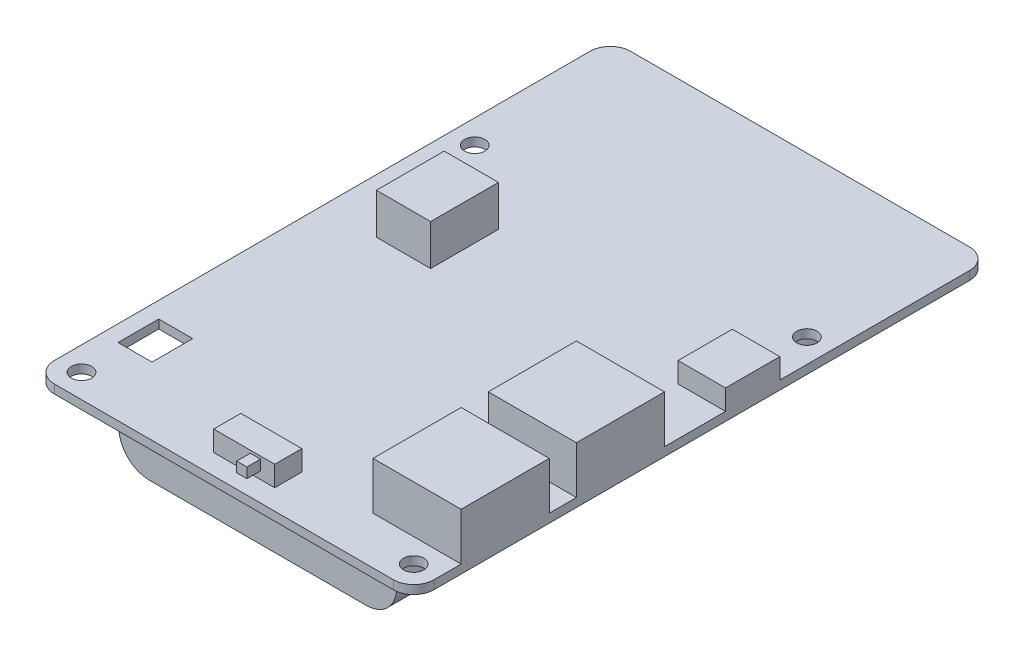
SolidWorks part; units mm, degrees
ref_plane "前基準面" through (0, 0, 0) normal (0, 0, 1) x (1, 0, 0)
ref_plane "上基準面" through (0, 0, 0) normal (0, 1, 0) x (1, 0, 0)
ref_plane "右基準面" through (0, 0, 0) normal (1, 0, 0) x (0, 0, -1)
sketch "草圖1" plane through (0, 0, 0) normal (0, 1, 0) x (1, 0, 0)
  line L1 (-28, -42.5) -> (28, -42.5)
  line L2 (-28, -42.5) -> (-28, 42.5)
  line L3 (-28, 42.5) -> (28, 42.5)
  line L4 (28, -42.5) -> (28, 42.5)
  line L5 (0, 42.5) -> (0, -42.5) construction
  line L6 (-28, 0) -> (28, 0) construction
  circle A0 centre (-24.5, 19) radius 1.5
  circle A1 centre (-24.5, -39) radius 1.5
  circle A2 centre (24.5, -39) radius 1.5
  circle A3 centre (24.5, 19) radius 1.5
  point P0 (0, 0)
  point P8 (0, 0)
  dimension "D3" = 3
  dimension "D1" = 56
  dimension "D2" = 85
  dimension "D4" = 58
  dimension "D5" = 49
  dimension "D6" = 3.5
extrude "填料-伸長1" add sketch "草圖1" along normal blind 1.28
fillet "圓角1" radius 3 4 edges at (-28, 0.64, -42.5) (28, 0.64, -42.5) (28, 0.64, 42.5) (-28, 0.64, 42.5)
sketch "草圖2" plane through (0, 1.28, 0) normal (0, 1, 0) x (1, 0, 0)
  line L0 (28, -39.5) -> (28, 39.5) construction
  line L7 (-25, -42.5) -> (25, -42.5) construction
  line L8 (15, -5.5) -> (28, -5.5)
  line L9 (15, -5.5) -> (15, -18.5)
  line L10 (15, -18.5) -> (28, -18.5)
  line L11 (28, -5.5) -> (28, -18.5)
  line L12 (21.5, -18.5) -> (21.5, -5.5) construction
  line L13 (15, -12) -> (28, -12) construction
  line L14 (15, -22.5) -> (28, -22.5)
  line L15 (15, -22.5) -> (15, -35.5)
  line L16 (15, -35.5) -> (28, -35.5)
  line L17 (28, -22.5) -> (28, -35.5)
  line L18 (21.5, -35.5) -> (21.5, -22.5) construction
  line L19 (15, -29) -> (28, -29) construction
  point P6 (21.5, -12)
  point P10 (21.5, -29)
  dimension "D1" = 13
  dimension "D2" = 13
  dimension "D3" = 13
  dimension "D4" = 13
  dimension "D5" = 30
  dimension "D6" = 7
sketch "草圖3" plane through (0, 1.28, 0) normal (0, 1, 0) x (1, 0, 0)
  line L0 (28, -39.5) -> (28, 39.5) construction
  line L1 (21, 11.5) -> (28, 11.5)
  line L2 (21, 11.5) -> (21, 3.5)
  line L3 (21, 3.5) -> (28, 3.5)
  line L4 (28, 11.5) -> (28, 3.5)
  line L5 (24.5, 3.5) -> (24.5, 11.5) construction
  line L6 (21, 7.5) -> (28, 7.5) construction
  line L7 (15, -5.5) -> (28, -5.5) construction
  point P0 (24.5, 7.5)
  dimension "D1" = 8
  dimension "D2" = 7
  dimension "D3" = 9
sketch "草圖4" plane through (0, 1.28, 0) normal (0, 1, 0) x (1, 0, 0)
  line L0 (-28, 39.5) -> (-28, -39.5) construction
  line L1 (-20, 10) -> (-12, 10)
  line L2 (-20, 10) -> (-20, 0)
  line L3 (-20, 0) -> (-12, 0)
  line L4 (-12, 10) -> (-12, 0)
  line L5 (-16, 0) -> (-16, 10) construction
  line L6 (-20, 5) -> (-12, 5) construction
  line L7 (25, 42.5) -> (-25, 42.5) construction
  point P0 (-16, 5)
  dimension "D1" = 8
  dimension "D2" = 10
  dimension "D3" = 8
  dimension "D4" = 32.5
sketch "草圖5" plane through (0, 1.28, 0) normal (0, 1, 0) x (1, 0, 0)
  line L0 (-25, -42.5) -> (25, -42.5) construction
  line L1 (-4.5, -35.5) -> (4.5, -35.5)
  line L2 (-4.5, -35.5) -> (-4.5, -39.5)
  line L3 (-4.5, -39.5) -> (4.5, -39.5)
  line L4 (4.5, -35.5) -> (4.5, -39.5)
  line L5 (0, -39.5) -> (0, -35.5) construction
  line L6 (-4.5, -37.5) -> (4.5, -37.5) construction
  point P0 (0, -37.5)
  dimension "D1" = 9
  dimension "D2" = 4
  dimension "D3" = 3
sketch "草圖6" plane through (0, 1.28, 0) normal (0, 1, 0) x (1, 0, 0)
  line L0 (-28, 39.5) -> (-28, -39.5) construction
  line L1 (-25.6, -26.5) -> (-20.6, -26.5)
  line L2 (-25.6, -26.5) -> (-25.6, -32.5)
  line L3 (-25.6, -32.5) -> (-20.6, -32.5)
  line L4 (-20.6, -26.5) -> (-20.6, -32.5)
  line L5 (-23.1, -32.5) -> (-23.1, -26.5) construction
  line L6 (-25.6, -29.5) -> (-20.6, -29.5) construction
  line L7 (-25, -42.5) -> (25, -42.5) construction
  point P0 (-23.1, -29.5)
  dimension "D1" = 5
  dimension "D2" = 6
  dimension "D3" = 2.4
  dimension "D4" = 10
extrude "除料-伸長1" cut sketch "草圖6" against normal through all
extrude "填料-伸長2" add sketch "草圖4" along normal blind 6
extrude "填料-伸長3" add sketch "草圖5" along normal blind 3
extrude "填料-伸長4" add sketch "草圖2" along normal blind 7
extrude "填料-伸長5" add sketch "草圖3" along normal blind 3
sketch "草圖7" plane through (0, 0, 39.5) normal (0, 0, 1) x (1, 0, 0)
  line L0 (-4.5, 4.28) -> (4.5, 4.28) construction
  line L1 (0.9, 3.88) -> (2.4, 3.88)
  line L2 (0.9, 3.88) -> (0.9, 2.38)
  line L3 (0.9, 2.38) -> (2.4, 2.38)
  line L4 (2.4, 3.88) -> (2.4, 2.38)
  line L5 (1.65, 2.38) -> (1.65, 3.88) construction
  line L6 (0.9, 3.13) -> (2.4, 3.13) construction
  line L7 (0, -8.6345) -> (0, 8.6345) construction
  point P0 (1.65, 3.13)
  point P9 (0, 0)
  dimension "D1" = 1.5
  dimension "D2" = 1.5
  dimension "D3" = 0.4
  dimension "D4" = 0.9
extrude "填料-伸長6" add sketch "草圖7" along normal blind 2
sketch "草圖9" plane through (0, 0, 0) normal (0, 0, 1) x (1, 0, 0)
  line L0 (0, -25.1378) -> (0, 25.1378) construction
  line L2 (-16, -4.5) -> (16, -4.5) construction
  line L3 (-16, 0) -> (16, 0)
  line L4 (-16, -9) -> (16, -9)
  line L5 (-25, 0) -> (25, 0) construction
  arc A0 (-16, 0) -> (-16, -9) centre (-16, -4.5) ccw
  arc A1 (16, -9) -> (16, 0) centre (16, -4.5) ccw
  point P5 (0, -4.5)
  point P6 (0, 0)
  dimension "D1" = 4.5
  dimension "D2" = 32
extrude "填料-伸長8" add sketch "草圖9" against normal blind 67 from offset 37.5
